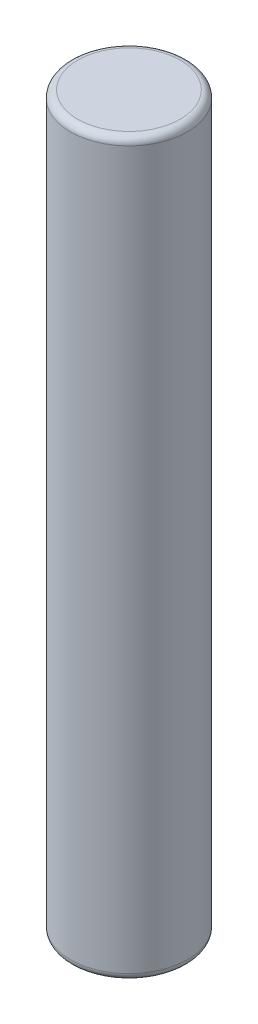
SolidWorks part; units mm, degrees
ref_plane "Front Plane" through (0, 0, 0) normal (0, 0, 1) x (1, 0, 0)
ref_plane "Top Plane" through (0, 0, 0) normal (0, 1, 0) x (1, 0, 0)
ref_plane "Right Plane" through (0, 0, 0) normal (1, 0, 0) x (0, 0, -1)
sketch "Sketch1" plane through (0, 0, 0) normal (0, 1, 0) x (1, 0, 0)
  circle A0 centre (0, 0) radius 4
  dimension "D1" = 8
extrude "Boss-Extrude1" add sketch "Sketch1" along normal blind 50
fillet "Fillet1" radius 0.5 2 edges at (0, 50, 4) (0, 0, 4)
